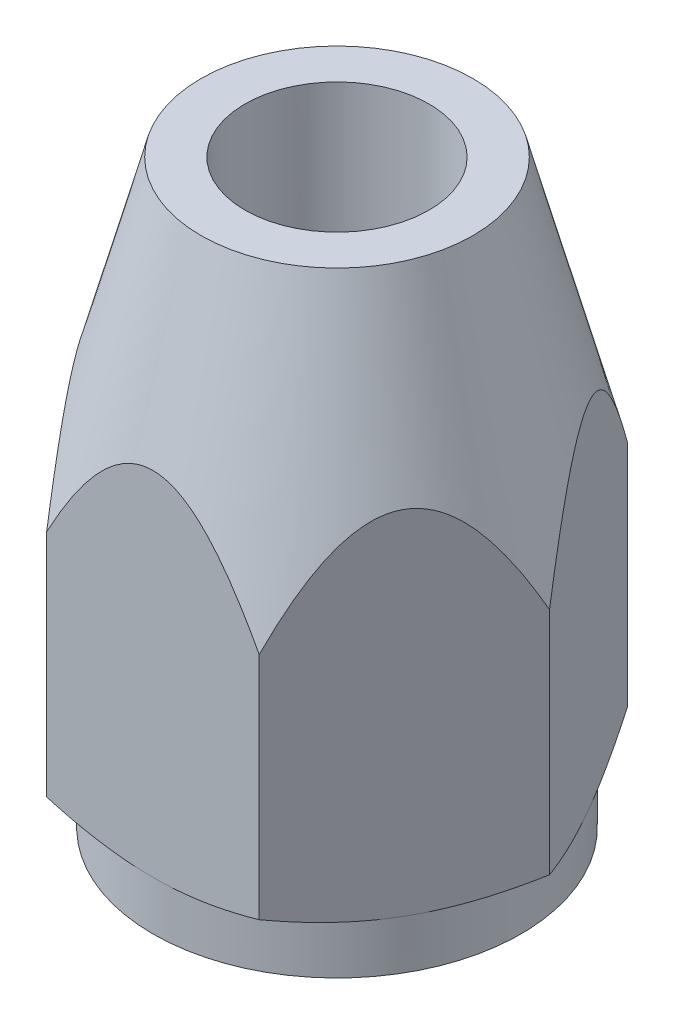
SolidWorks part; units mm, degrees
ref_plane "Front Plane" through (0, 0, 0) normal (0, 0, 1) x (1, 0, 0)
ref_plane "Top Plane" through (0, 0, 0) normal (0, 1, 0) x (1, 0, 0)
ref_plane "Right Plane" through (0, 0, 0) normal (1, 0, 0) x (0, 0, -1)
sketch "Sketch1" plane through (0, 0, 0) normal (0, 1, 0) x (1, 0, 0)
  line L1 (-2.5981, -4.5) -> (2.5981, -4.5)
  line L2 (2.5981, -4.5) -> (5.1962, 0)
  line L3 (5.1962, 0) -> (2.5981, 4.5)
  line L4 (2.5981, 4.5) -> (-2.5981, 4.5)
  line L5 (-2.5981, 4.5) -> (-5.1962, 0)
  line L6 (-5.1962, 0) -> (-2.5981, -4.5)
  circle A0 centre (0, 0) radius 4.5 construction
  dimension "D1" = 9
extrude "Boss-Extrude1" add sketch "Sketch1" along normal blind 14.2
sketch "Sketch2" plane through (0, 14.2, 0) normal (0, 1, 0) x (1, 0, 0)
  circle A0 centre (0, 0) radius 2.25
  dimension "D1" = 4.5
extrude "Cut-Extrude1" cut sketch "Sketch2" against normal through all
sketch "Sketch3" plane through (0, 0, 0) normal (0, -1, 0) x (1, 0, 0)
  circle A0 centre (0, 0) radius 3.95
  dimension "D1" = 7.9
extrude "Cut-Extrude2" cut sketch "Sketch3" against normal blind 10
sketch "Sketch4" plane through (0, 14.2, 0) normal (0, 1, 0) x (1, 0, 0)
  circle A0 centre (0, 0) radius 3.325
  dimension "D1" = 6.65
extrude "Cut-Extrude3" cut sketch "Sketch4" against normal blind 10 draft 15 flip side to cut
sketch "Sketch5" plane through (0, 0, 0) normal (0, -1, 0) x (1, 0, 0)
  circle A0 centre (0, 0) radius 4.5
extrude "Cut-Extrude4" cut sketch "Sketch5" against normal blind 1.2 flip side to cut
sketch "Sketch6" plane through (0, 1.2, 0) normal (0, -1, 0) x (1, 0, 0)
  circle A2 centre (0, 0) radius 4.5
  circle A3 centre (0, 0) radius 4.5
  dimension "D1" = 0
extrude "Cut-Extrude5" cut sketch "Sketch6" against normal blind 10 draft 60 flip side to cut
sketch "Sketch7" plane through (0, 14.2, 0) normal (0, 1, 0) x (1, 0, 0)
  point P0 (0, 0)
